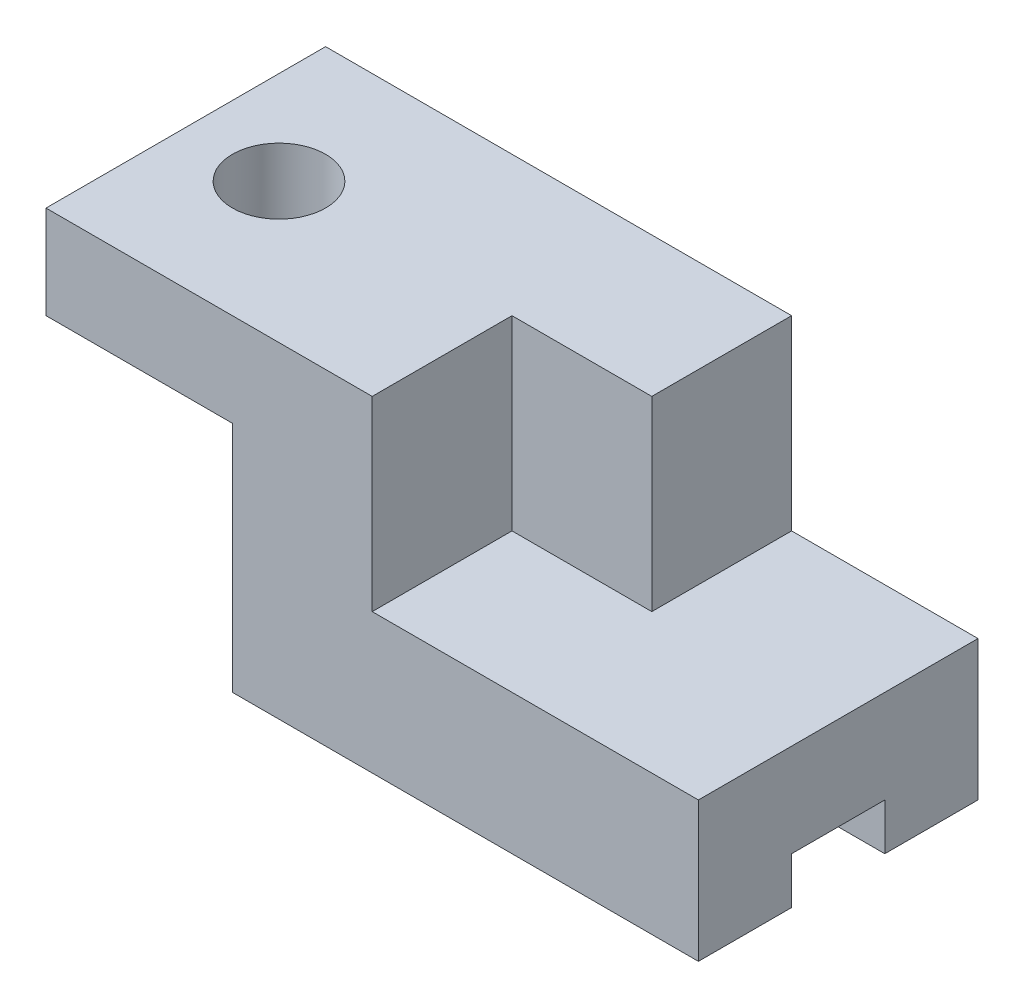
SolidWorks part; units mm, degrees
ref_plane "Front Plane" through (0, 0, 0) normal (0, 0, 1) x (1, 0, 0)
ref_plane "Top Plane" through (0, 0, 0) normal (0, 1, 0) x (1, 0, 0)
ref_plane "Right Plane" through (0, 0, 0) normal (1, 0, 0) x (0, 0, -1)
sketch "Sketch1" plane through (0, 0, 0) normal (0, 1, 0) x (1, 0, 0)
  line L1 (0, 0) -> (70, 0)
  line L2 (0, 0) -> (0, 30)
  line L3 (0, 30) -> (70, 30)
  line L4 (70, 0) -> (70, 30)
  dimension "D1" = 70
  dimension "D2" = 30
extrude "Boss-Extrude1" add sketch "Sketch1" along normal blind 35
sketch "Sketch2" plane through (0, 35, 0) normal (0, 1, 0) x (1, 0, 0)
  line L0 (70, 30) -> (50, 30)
  line L1 (70, 30) -> (0, 30) construction
  line L2 (50, 30) -> (50, 15)
  line L3 (50, 15) -> (35, 15)
  line L4 (35, 15) -> (35, 0)
  line L5 (0, 0) -> (70, 0) construction
  line L6 (35, 0) -> (70, 0)
  line L7 (70, 0) -> (70, 30)
  dimension "D1" = 20
extrude "Cut-Extrude1" cut sketch "Sketch2" against normal blind 20
sketch "Sketch3" plane through (0, 0, 0) normal (0, 0, 1) x (1, 0, 0)
  line L0 (0, 0) -> (0, 25)
  line L1 (0, 35) -> (0, 0) construction
  line L2 (0, 25) -> (20, 25)
  line L3 (20, 25) -> (20, 0)
  line L4 (0, 0) -> (70, 0) construction
  line L5 (20, 0) -> (0, 0)
  dimension "D1" = 20
  dimension "D2" = 25
extrude "Cut-Extrude2" cut sketch "Sketch3" against normal through all
sketch "Sketch4" plane through (0, 35, 0) normal (0, 1, 0) x (1, 0, 0)
  line L0 (0, 15) -> (10, 15) construction
  line L1 (0, 30) -> (0, 0) construction
  circle A0 centre (10, 15) radius 5
  dimension "D2" = 10
  dimension "D1" = 10
extrude "Cut-Extrude3" cut sketch "Sketch4" against normal through all contours A0
sketch "Sketch5" plane through (70, 0, 0) normal (1, 0, 0) x (0, 0, -1)
  line L0 (0, 0) -> (10, 0) construction
  line L1 (0, 0) -> (30, 0) construction
  line L3 (10, 0) -> (20, 0)
  line L4 (10, 0) -> (10, 5)
  line L5 (10, 5) -> (20, 5)
  line L6 (20, 0) -> (20, 5)
  dimension "D1" = 10
  dimension "D2" = 5
  dimension "D3" = 10
extrude "Cut-Extrude4" cut sketch "Sketch5" against normal through all contours L4 L3 L6 L5
